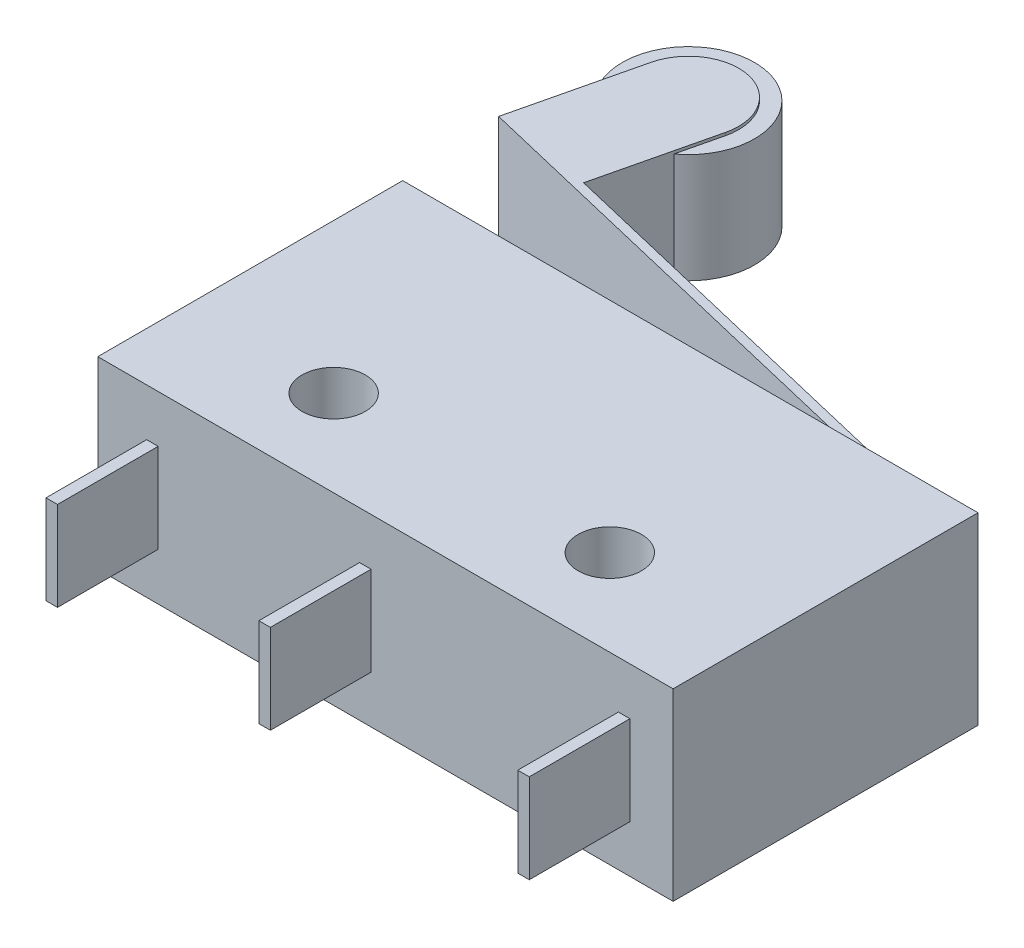
SolidWorks part; units mm, degrees
ref_plane "前视基准面" through (0, 0, 0) normal (0, 0, 1) x (1, 0, 0)
ref_plane "上视基准面" through (0, 0, 0) normal (0, 1, 0) x (1, 0, 0)
ref_plane "右视基准面" through (0, 0, 0) normal (1, 0, 0) x (0, 0, -1)
sketch "草图1" plane through (0, 0, 0) normal (0, 1, 0) x (1, 0, 0)
  line L1 (-10, -5.3) -> (10, -5.3)
  line L2 (-10, -5.3) -> (-10, 5.3)
  line L3 (-10, 5.3) -> (10, 5.3)
  line L4 (10, -5.3) -> (10, 5.3)
  line L5 (-10, -5.3) -> (10, 5.3) construction
  line L6 (-10, 5.3) -> (10, -5.3) construction
  circle A0 centre (-4.8, -2.3) radius 1.1
  circle A1 centre (4.8, -2.3) radius 1.1
  point P0 (0, 0)
  dimension "D3" = 2.2
  dimension "D1" = 20
  dimension "D2" = 10.6
  dimension "D4" = 3
  dimension "D5" = 5.2
  dimension "D6" = 5.2
extrude "凸台-拉伸1" add sketch "草图1" along normal mid plane 6.4
sketch "草图3" plane through (0, 0, 5.3) normal (0, 0, 1) x (1, 0, 0)
  line L0 (-13.199, 0) -> (13.199, 0) construction
  line L2 (-8.3, -1.55) -> (-7.9, -1.55)
  line L3 (-8.3, -1.55) -> (-8.3, 1.55)
  line L4 (-8.3, 1.55) -> (-7.9, 1.55)
  line L5 (-7.9, -1.55) -> (-7.9, 1.55)
  line L6 (-8.3, -1.55) -> (-7.9, 1.55) construction
  line L7 (-8.3, 1.55) -> (-7.9, -1.55) construction
  line L8 (-0.9, -1.55) -> (-0.5, -1.55)
  line L9 (-0.9, -1.55) -> (-0.9, 1.55)
  line L10 (-0.9, 1.55) -> (-0.5, 1.55)
  line L11 (-0.5, -1.55) -> (-0.5, 1.55)
  line L12 (-0.9, -1.55) -> (-0.5, 1.55) construction
  line L13 (-0.9, 1.55) -> (-0.5, -1.55) construction
  line L14 (8.1, -1.55) -> (8.5, -1.55)
  line L15 (8.1, -1.55) -> (8.1, 1.55)
  line L16 (8.1, 1.55) -> (8.5, 1.55)
  line L17 (8.5, -1.55) -> (8.5, 1.55)
  line L18 (8.1, -1.55) -> (8.5, 1.55) construction
  line L19 (8.1, 1.55) -> (8.5, -1.55) construction
  line L20 (-10, 3.2) -> (-10, -3.2) construction
  line L21 (10, 3.2) -> (10, -3.2) construction
  point P0 (-8.1, 0)
  point P4 (0, 0)
  point P9 (-0.7, 0)
  point P14 (8.3, 0)
  dimension "D1" = 3.1
  dimension "D2" = 0.4
  dimension "D3" = 1.7
  dimension "D4" = 7.8
  dimension "D5" = 1.5
extrude "凸台-拉伸2" add sketch "草图3" along normal blind 3.5
sketch "草图4" plane through (0, 0, 0) normal (0, 1, 0) x (1, 0, 0)
  line L0 (6.3, 4.6625) -> (6.3, 5.8631)
  line L1 (6.3, 5.8631) -> (-11.4649, 10.1)
  line L2 (-11.4649, 10.1) -> (-10.4441, 14.38)
  line L3 (10, -5.3) -> (10, 5.3) construction
  line L4 (-7.0396, 13.568) -> (-7.9908, 9.5799)
  line L5 (-7.9908, 9.5799) -> (6.6, 6.1)
  line L6 (6.6, 6.1) -> (6.6, 4.6625)
  line L7 (6.6, 4.6625) -> (6.3, 4.6625)
  line L8 (10, 5.3) -> (-10, 5.3) construction
  arc A0 (-10.4441, 14.38) -> (-7.0396, 13.568) centre (-8.7419, 13.974) cw
  dimension "D1" = 3.5
  dimension "D2" = 0.3
  dimension "D3" = 0.3
  dimension "D4" = 18.5
  dimension "D5" = 3.4
  dimension "D6" = 0.8
  dimension "D7" = 4.8
  dimension "D8" = 4.4
extrude "凸台-拉伸3" add sketch "草图4" along normal mid plane 4
sketch "草图5" plane through (0, 0, 0) normal (0, 1, 0) x (1, 0, 0)
  circle A0 centre (-8.7419, 13.974) radius 2.3
  dimension "D1" = 4.6
extrude "凸台-拉伸4" add sketch "草图5" along normal mid plane 3.8
